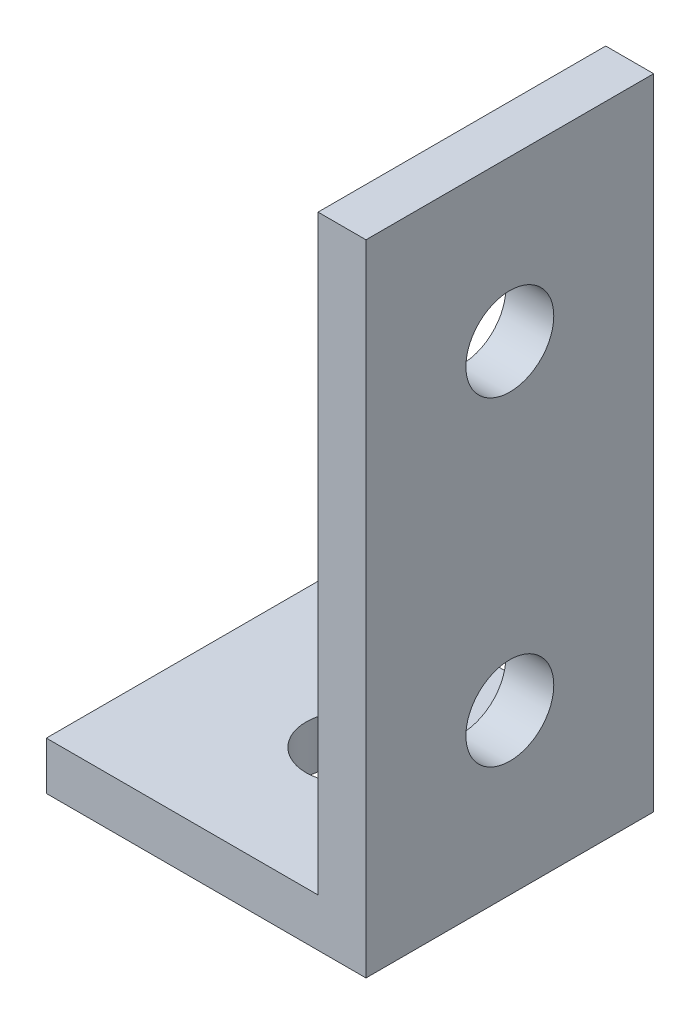
SolidWorks part; units mm, degrees
ref_plane "前视基准面" through (0, 0, 0) normal (0, 0, 1) x (1, 0, 0)
ref_plane "上视基准面" through (0, 0, 0) normal (0, 1, 0) x (1, 0, 0)
ref_plane "右视基准面" through (0, 0, 0) normal (1, 0, 0) x (0, 0, -1)
sketch "草图1" plane through (0, 0, 0) normal (0, 1, 0) x (1, 0, 0)
  line L1 (10, -9) -> (-10, -9)
  line L2 (10, -9) -> (10, 9)
  line L3 (10, 9) -> (-10, 9)
  line L4 (-10, -9) -> (-10, 9)
  line L5 (10, -9) -> (-10, 9) construction
  line L6 (10, 9) -> (-10, -9) construction
  point P0 (0, 0)
  dimension "D1" = 20
  dimension "D2" = 18
extrude "凸台-拉伸1" add sketch "草图1" along normal blind 3
sketch "草图2" plane through (0, 3, 0) normal (0, 1, 0) x (1, 0, 0)
  line L0 (10, -9) -> (10, 9)
  line L1 (10, 9) -> (7, 9)
  line L2 (10, 9) -> (-10, 9) construction
  line L3 (7, 9) -> (7, -9)
  line L4 (-10, -9) -> (10, -9) construction
  line L5 (7, -9) -> (10, -9)
  dimension "D1" = 3
extrude "凸台-拉伸2" add sketch "草图2" along normal blind 37
sketch "草图4" plane through (0, 0, 0) normal (0, -1, 0) x (1, 0, 0)
  line L0 (-10, 9) -> (10, 9) construction
  line L1 (10, 9) -> (10, -9) construction
  circle A0 centre (0, 0) radius 2.75
  dimension "D1" = 9
  dimension "D2" = 10
extrude "切除-拉伸1" cut sketch "草图4" against normal through all
sketch "草图5" plane through (10, 0, 0) normal (1, 0, 0) x (0, 0, -1)
  line L0 (-9, 0) -> (9, 0) construction
  circle A0 centre (0, 10) radius 2.75
  circle A1 centre (0, 30) radius 2.75
  dimension "D1" = 10
  dimension "D2" = 20
extrude "切除-拉伸2" cut sketch "草图5" against normal through all
equation "\"10‘\"=1"
